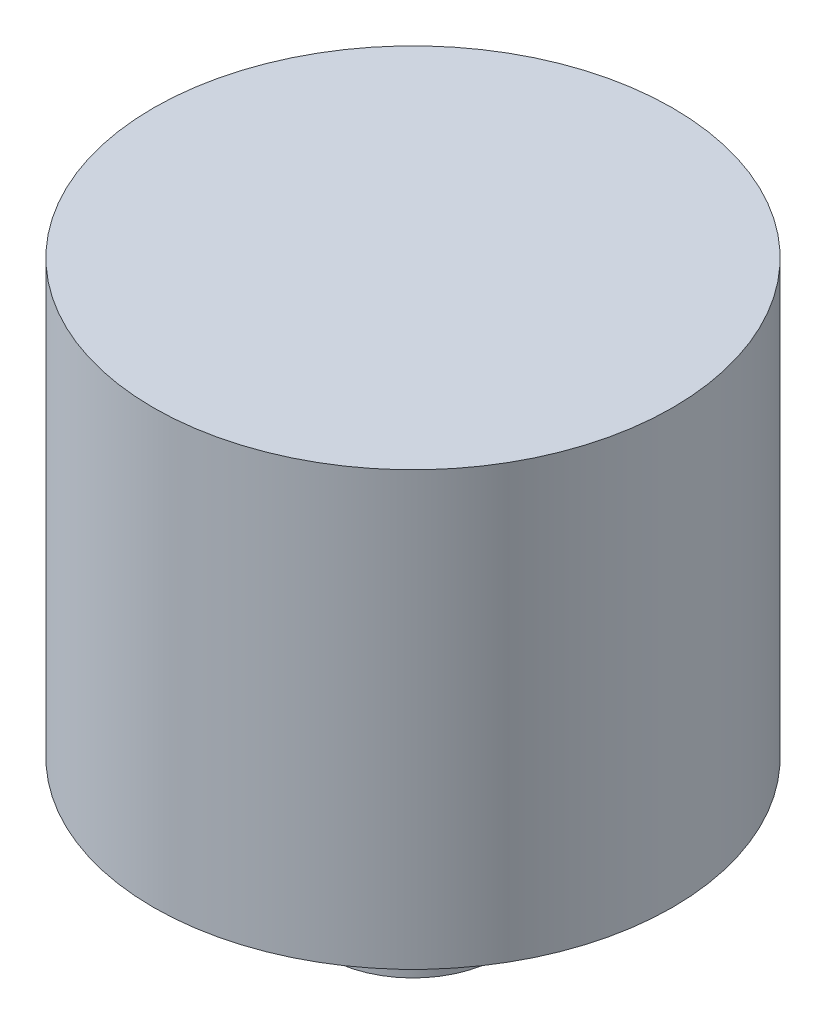
SolidWorks part; units mm, degrees
ref_plane "Front Plane" through (0, 0, 0) normal (0, 0, 1) x (1, 0, 0)
ref_plane "Top Plane" through (0, 0, 0) normal (0, 1, 0) x (1, 0, 0)
ref_plane "Right Plane" through (0, 0, 0) normal (1, 0, 0) x (0, 0, -1)
sketch "Sketch1" plane through (0, 0, 0) normal (0, 0, 1) x (1, 0, 0)
  line L0 (0, 0) -> (-2, 0)
  line L1 (-2, 0) -> (-2, 3)
  line L2 (-2, 3) -> (-6, 3)
  line L3 (-6, 3) -> (-6, 13)
  line L4 (-6, 13) -> (0, 13)
  line L5 (0, 13) -> (0, 0)
  dimension "D1" = 2
  dimension "D2" = 3
  dimension "D3" = 6
  dimension "D4" = 10
revolve "Revolve1" add sketch "Sketch1" angle 360 about L5
